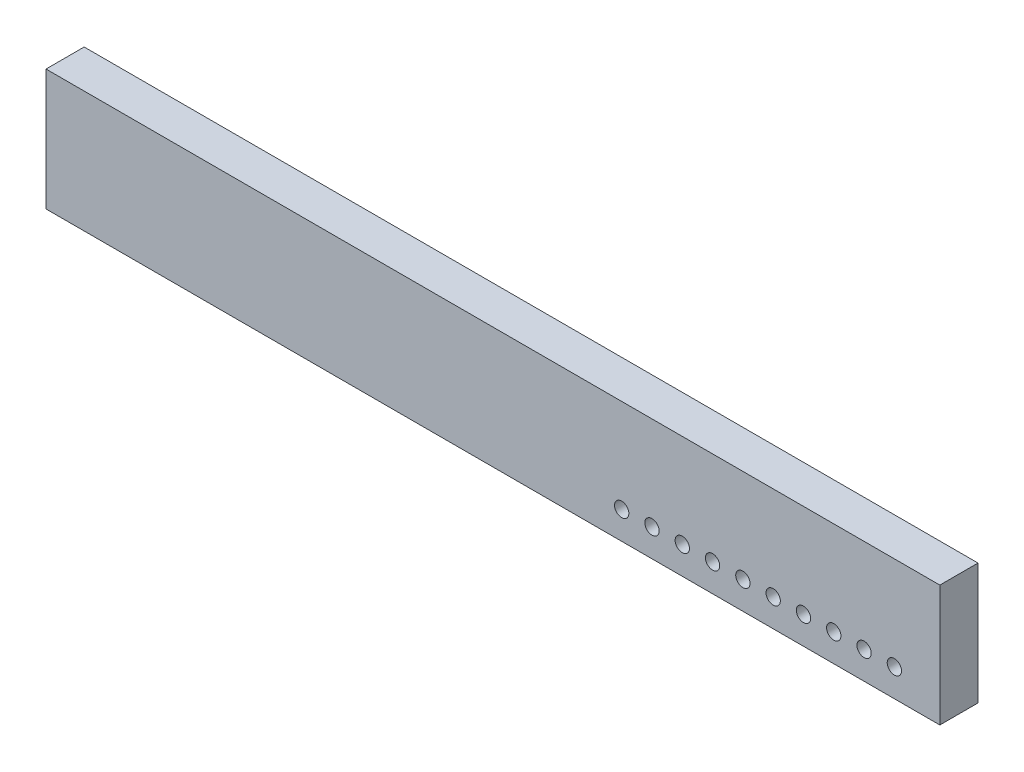
SolidWorks part; units mm, degrees
ref_plane "Front Plane" through (0, 0, 0) normal (0, 0, 1) x (1, 0, 0)
ref_plane "Top Plane" through (0, 0, 0) normal (0, 1, 0) x (1, 0, 0)
ref_plane "Right Plane" through (0, 0, 0) normal (1, 0, 0) x (0, 0, -1)
sketch "Sketch1" plane through (0, 0, 0) normal (0, 0, 1) x (1, 0, 0)
  line L1 (-18.7325, -2.54) -> (18.7325, -2.54)
  line L2 (-18.7325, -2.54) -> (-18.7325, 2.54)
  line L3 (-18.7325, 2.54) -> (18.7325, 2.54)
  line L4 (18.7325, -2.54) -> (18.7325, 2.54)
  line L5 (-18.7325, -2.54) -> (18.7325, 2.54) construction
  line L6 (-18.7325, 2.54) -> (18.7325, -2.54) construction
  point P0 (0, 0)
  dimension "D1" = 37.465
  dimension "D2" = 5.08
extrude "Boss-Extrude1" add sketch "Sketch1" along normal blind 1.6
sketch "Sketch2" plane through (0, 0, 1.6) normal (0, 0, 1) x (1, 0, 0)
  line L0 (5.4725, -1.455) -> (5.3225, -1.305) construction
  line L4 (5.3225, -1.455) -> (5.4725, -1.455)
  line L5 (5.4725, -1.455) -> (5.4725, -1.305)
  line L6 (5.4725, -1.305) -> (5.3225, -1.305)
  line L7 (5.3225, -1.305) -> (5.3225, -1.455)
  line L8 (5.3225, -1.455) -> (5.4725, -1.455)
  line L9 (5.4725, -1.455) -> (5.4725, -1.305)
  line L10 (5.4725, -1.305) -> (5.3225, -1.305)
  line L11 (5.3225, -1.305) -> (5.3225, -1.455)
  circle A0 centre (5.3975, -1.38) radius 0.3
  circle A1 centre (6.6675, -1.38) radius 0.3
  circle A2 centre (7.9375, -1.38) radius 0.3
  circle A3 centre (9.2075, -1.38) radius 0.3
  circle A4 centre (10.4775, -1.38) radius 0.3
  circle A5 centre (11.7475, -1.38) radius 0.3
  circle A6 centre (13.0175, -1.38) radius 0.3
  circle A7 centre (14.2875, -1.38) radius 0.3
  circle A8 centre (15.5575, -1.38) radius 0.3
  circle A9 centre (16.8275, -1.38) radius 0.3
  dimension "D2" = 0.6
  dimension "D1" = 0
  dimension "D3" = 10
extrude "Cut-Extrude3" cut sketch "Sketch2" against normal through all
